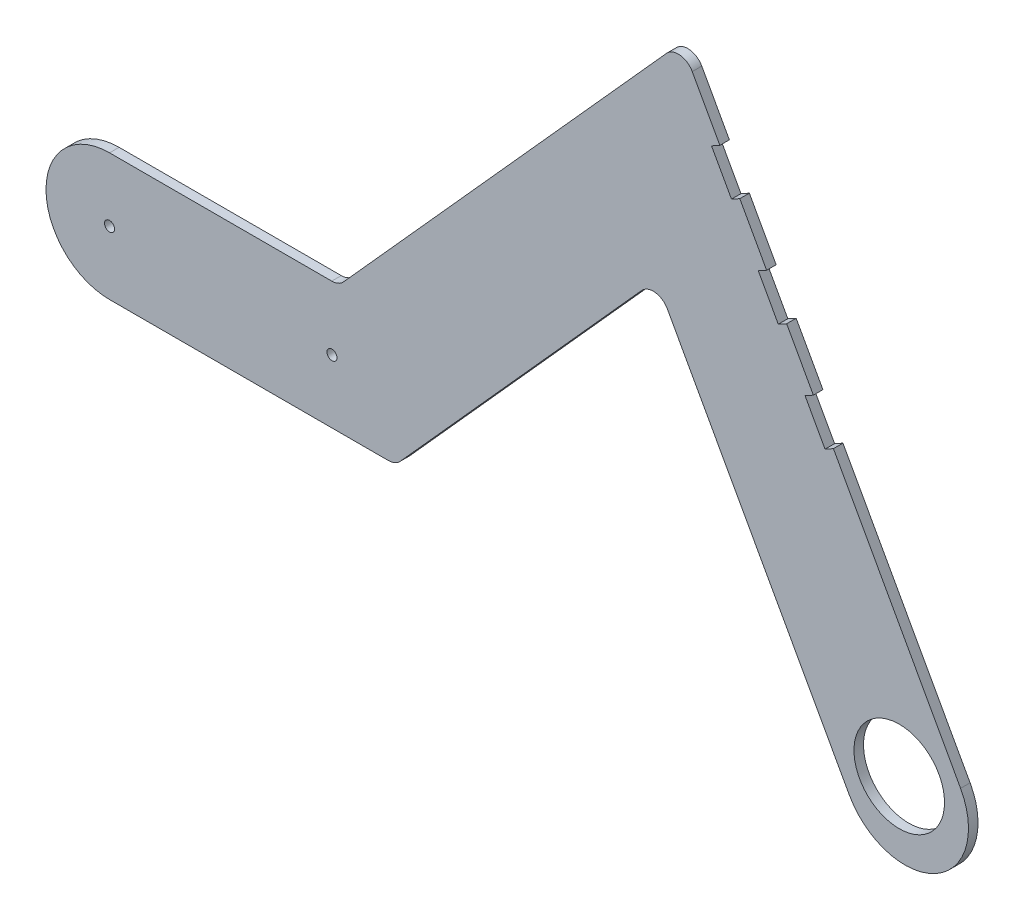
SolidWorks part; units mm, degrees
ref_plane "Front Plane" through (0, 0, 0) normal (0, 0, 1) x (1, 0, 0)
ref_plane "Top Plane" through (0, 0, 0) normal (0, 1, 0) x (1, 0, 0)
ref_plane "Right Plane" through (0, 0, 0) normal (1, 0, 0) x (0, 0, -1)
sketch "Croquis1" plane through (0, 0, 0) normal (0, 0, 1) x (1, 0, 0)
  line L0 (-135.8112, 31.6609) -> (-65.8732, 31.6609)
  line L1 (-62.1542, 33.3189) -> (39.488, 146.4297)
  line L2 (47.5853, 145.5024) -> (132.0431, -7.6343)
  line L3 (97.017, -26.9519) -> (39.7313, 76.9171)
  line L4 (31.634, 77.8443) -> (-44.3213, -6.6811)
  line L5 (-48.0403, -8.3391) -> (-135.8112, -8.3391)
  arc A0 (132.0431, -7.6343) -> (97.017, -26.9519) centre (114.53, -17.2931) cw
  arc A1 (-135.8112, -8.3391) -> (-135.8112, 31.6609) centre (-135.8112, 11.6609) cw
  circle A3 centre (-135.8112, 11.6609) radius 1.58
  circle A4 centre (-65.8112, 11.5885) radius 1.58
  circle A6 centre (112.7386, -14.0449) radius 14.25
  arc A7 (-62.1542, 33.3189) -> (-65.8732, 31.6609) centre (-65.8732, 36.6609) cw
  arc A8 (47.5853, 145.5024) -> (39.488, 146.4297) centre (43.2071, 143.0877) ccw
  arc A9 (39.7313, 76.9171) -> (31.634, 77.8443) centre (35.353, 74.5024) ccw
  arc A10 (-44.3213, -6.6811) -> (-48.0403, -8.3391) centre (-48.0403, -3.3391) cw
  point P17 (-155.8112, 11.6609)
  point P18 (124.1888, -34.8061)
  point P22 (44.1888, 151.6609)
  point P27 (-45.8112, -8.3391)
  dimension "D10" = 3.16
  dimension "D11" = 28.5
  dimension "D13" = 5
  dimension "D1" = 40
  dimension "D2" = 40
  dimension "D3" = 40
  dimension "D4" = 70
  dimension "D5" = 90
  dimension "D6" = 280
  dimension "D7" = 46.467
  dimension "D8" = 90
  dimension "D9" = 120
  dimension "D12" = 20
extrude "Saliente-Extruir1" add sketch "Croquis1" along normal blind 3
sketch "Croquis3" plane through (98.0182, 54.0589, 0) normal (0.8757, 0.4829, 0) x (0, 0, -1)
  line L0 (-3, -70.4538) -> (-3, 104.4289) construction
  line L1 (-3, 86.4289) -> (0, 86.4289)
  line L2 (-3, 86.4289) -> (-3, 73.4264)
  line L3 (-3, 73.4264) -> (0, 73.4264)
  line L4 (0, 86.4289) -> (0, 73.4264)
  line L5 (0, 86.4289) -> (-3, 86.4289) construction
  line L6 (0, -70.4538) -> (0, 104.4289) construction
  line L7 (0, 55.953) -> (-3, 55.953) construction
  line L8 (-3, 55.953) -> (0, 55.953)
  line L9 (-3, 55.953) -> (-3, 42.9048)
  line L10 (-3, 42.9048) -> (0, 42.9048)
  line L11 (0, 55.953) -> (0, 42.9048)
  line L12 (0, 42.9048) -> (-3, 42.9048) construction
  line L13 (0, 25.4771) -> (-3, 25.4771) construction
  line L14 (-3, 25.4771) -> (0, 25.4771)
  line L15 (-3, 25.4771) -> (-3, 12.4289)
  line L16 (-3, 12.4289) -> (0, 12.4289)
  line L17 (0, 25.4771) -> (0, 12.4289)
  line L18 (0, 12.4289) -> (-3, 12.4289) construction
extrude "Cortar-Extruir1" cut sketch "Croquis3" against normal blind 3
